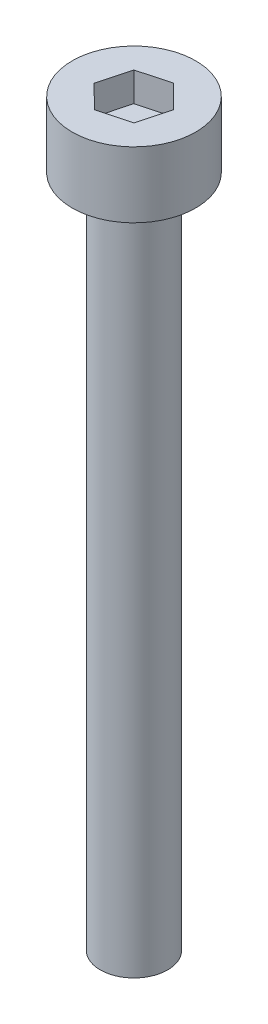
SolidWorks part; units mm, degrees
ref_plane "前视基准面" through (0, 0, 0) normal (0, 0, 1) x (1, 0, 0)
ref_plane "上视基准面" through (0, 0, 0) normal (0, 1, 0) x (1, 0, 0)
ref_plane "右视基准面" through (0, 0, 0) normal (1, 0, 0) x (0, 0, -1)
sketch "草图1" plane through (0, 0, 0) normal (0, 1, 0) x (1, 0, 0)
  circle A0 centre (0, 0) radius 1.5
  dimension "D1" = 3
extrude "凸台-拉伸1" add sketch "草图1" along normal blind 30
sketch "草图2" plane through (0, 30, 0) normal (0, 1, 0) x (1, 0, 0)
  circle A0 centre (0, 0) radius 2.75
  dimension "D1" = 5.5
extrude "凸台-拉伸2" add sketch "草图2" along normal blind 2.93
sketch "草图3" plane through (0, 32.93, 0) normal (0, 1, 0) x (1, 0, 0)
  line L1 (1.024, -1.0172) -> (1.3929, 0.3782)
  line L2 (1.3929, 0.3782) -> (0.3689, 1.3954)
  line L3 (0.3689, 1.3954) -> (-1.024, 1.0172)
  line L4 (-1.024, 1.0172) -> (-1.3929, -0.3782)
  line L5 (-1.3929, -0.3782) -> (-0.3689, -1.3954)
  line L6 (-0.3689, -1.3954) -> (1.024, -1.0172)
  circle A0 centre (0, 0) radius 1.25 construction
  dimension "D1" = 2.5
extrude "切除-拉伸1" cut sketch "草图3" against normal blind 1.3
